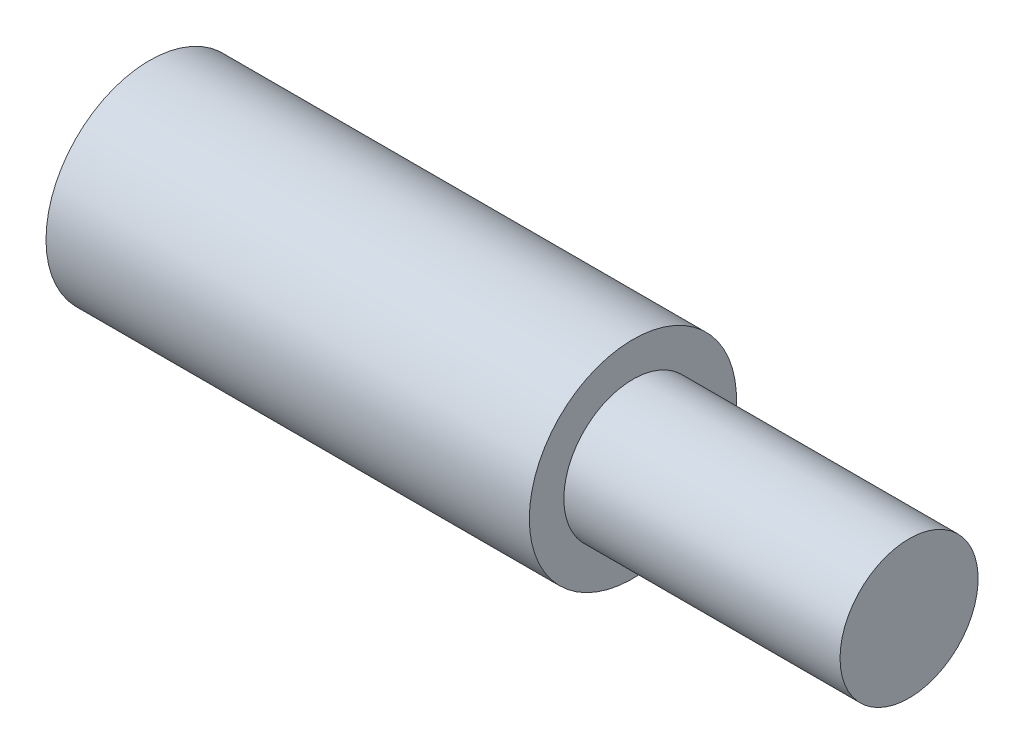
SolidWorks part; units mm, degrees
ref_plane "Front Plane" through (0, 0, 0) normal (0, 0, 1) x (1, 0, 0)
ref_plane "Top Plane" through (0, 0, 0) normal (0, 1, 0) x (1, 0, 0)
ref_plane "Right Plane" through (0, 0, 0) normal (1, 0, 0) x (0, 0, -1)
sketch "Sketch1" plane through (0, 0, 0) normal (0, 0, 1) x (1, 0, 0)
  line L0 (0, 0) -> (0, 1.5)
  line L1 (0, 1.5) -> (7, 1.5)
  line L2 (7, 1.5) -> (7, 1)
  line L3 (7, 1) -> (11, 1)
  line L4 (11, 1) -> (11, 0)
  line L5 (11, 0) -> (0, 0)
  line L6 (0, 0) -> (14.0217, 0) construction
  dimension "D1" = 3
  dimension "D2" = 7
  dimension "D3" = 4
  dimension "D4" = 2
revolve "Revolve1" add sketch "Sketch1" angle 360 about L6
